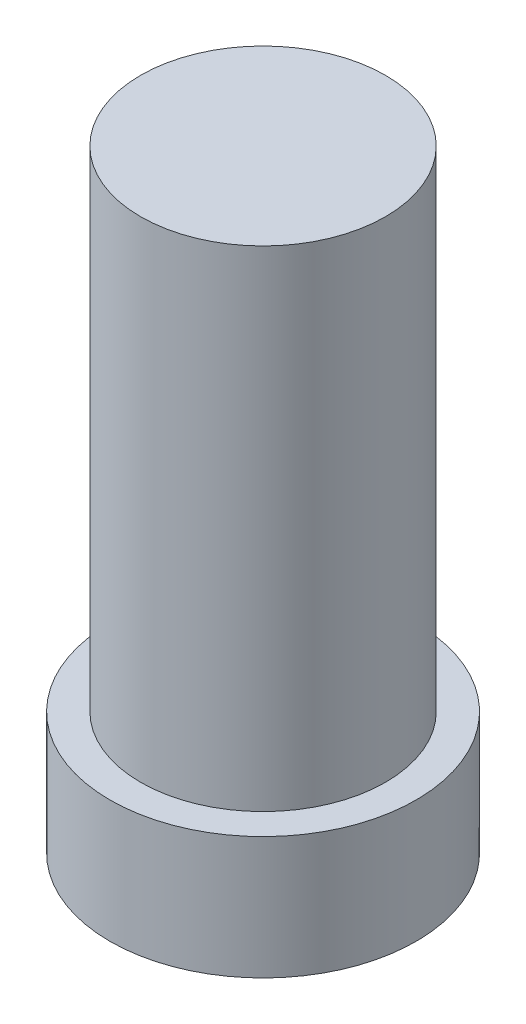
SolidWorks part; units mm, degrees
ref_plane "Front Plane" through (0, 0, 0) normal (0, 0, 1) x (1, 0, 0)
ref_plane "Top Plane" through (0, 0, 0) normal (0, 1, 0) x (1, 0, 0)
ref_plane "Right Plane" through (0, 0, 0) normal (1, 0, 0) x (0, 0, -1)
sketch "Sketch1" plane through (0, 0, 0) normal (0, 1, 0) x (1, 0, 0)
  circle A0 centre (0, 0) radius 2.5
  dimension "D1" = 5
extrude "Boss-Extrude1" add sketch "Sketch1" along normal blind 2
sketch "Sketch2" plane through (0, 2, 0) normal (0, 1, 0) x (1, 0, 0)
  circle A0 centre (0, 0) radius 2
  dimension "D1" = 4
extrude "Boss-Extrude2" add sketch "Sketch2" along normal blind 8
scale "Scale1" scale about centroid uniform scaling yes scale factor 0.225
